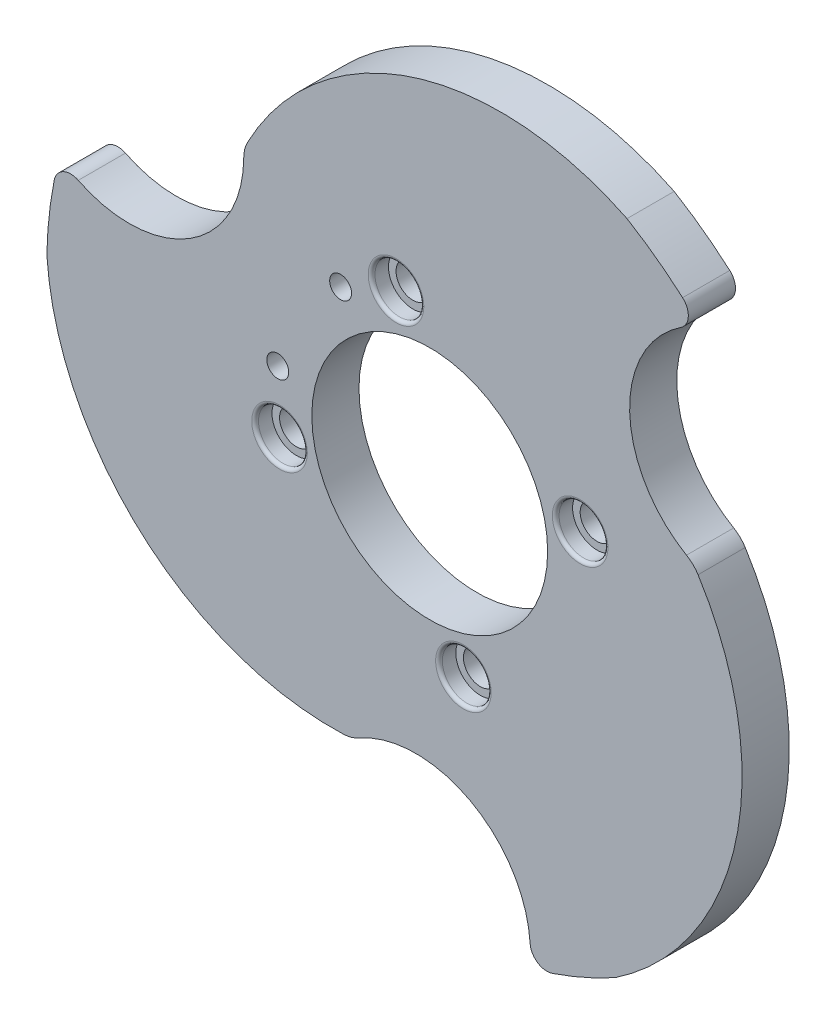
SolidWorks part; units mm, degrees
material "Nylon 101"
ref_plane "Front Plane" through (0, 0, 0) normal (0, 0, 1) x (1, 0, 0)
ref_plane "Top Plane" through (0, 0, 0) normal (0, 1, 0) x (1, 0, 0)
ref_plane "Right Plane" through (0, 0, 0) normal (1, 0, 0) x (0, 0, -1)
sketch "Sketch4" plane through (0, 0, 0) normal (0, 0, 1) x (1, 0, 0)
  line L0 (122.0825, 116.3897) -> (192.0825, 116.3897) construction
  line L1 (146.7212, 160.5313) -> (166.7236, 71.2444) construction
  arc A0 (231.7786, 201.237) -> (215.2728, 213.3033) centre (156.7224, 115.8878) ccw
  circle A1 centre (156.7224, 115.8878) radius 35
  arc A4 (102.6735, 176.6494) -> (215.2728, 213.3033) centre (177.8511, 136.9841) cw
  arc A5 (215.2728, 213.3033) -> (236.97, 196.3753) centre (156.7224, 115.8878) cw
  arc A7 (231.2424, 193.3169) -> (232.9372, 135.6297) centre (250.0433, 165.0007) ccw
  circle A8 centre (156.7224, 115.8878) radius 45.75 construction
  circle A9 centre (201.3658, 125.889) radius 5
  circle A10 centre (130.2738, 153.2179) radius 3.25
  circle A11 centre (166.7236, 71.2444) radius 5
  circle A12 centre (112.1469, 105.5881) radius 5
  circle A13 centre (146.7212, 160.5313) radius 5
  arc A14 (231.7786, 201.237) -> (231.2424, 193.3169) centre (228.4767, 197.4823) cw
  circle A15 centre (111.6251, 123.5881) radius 3.25
  arc A16 (186.5179, 12.637) -> (135.712, 40.0129) centre (152.595, 10.5131) ccw
  arc A17 (193.1088, 8.2126) -> (186.5179, 12.637) centre (191.5081, 12.9495) cw
  arc A18 (236.3679, 132.3147) -> (211.8114, 16.474) centre (164.428, 87.0417) cw
  arc A19 (193.1088, 8.2126) -> (211.8114, 16.474) centre (156.7224, 115.8878) ccw
  arc A20 (52.4068, 141.7095) -> (101.518, 172.0208) centre (67.5289, 172.1496) ccw
  arc A21 (45.2797, 138.2138) -> (52.4068, 141.7095) centre (50.1823, 137.2317) cw
  arc A22 (131.1257, 38.6993) -> (43.0829, 117.8862) centre (127.8881, 123.6376) cw
  arc A23 (45.2797, 138.2138) -> (43.0829, 117.8862) centre (156.7224, 115.8878) ccw
  arc A24 (232.9372, 135.6297) -> (236.3679, 132.3147) centre (227.9044, 126.9885) cw
  arc A25 (102.6735, 176.6494) -> (101.518, 172.0208) centre (111.5179, 171.9829) ccw
  arc A26 (135.712, 40.0129) -> (131.1257, 38.6993) centre (130.7448, 48.692) cw
  point P2 (236.97, 196.3753)
  point P3 (45.5812, 139.6691)
  point P4 (191.688, 7.7429)
  point P6 (48.1945, 141.391)
  point P8 (233.1808, 195.9929)
  point P9 (46.4024, 140.5065)
  point P10 (50.4833, 141.391)
  point P11 (53.7133, 140.5065)
  point P12 (58.5618, 139.2257)
  point P13 (61.9304, 138.4246)
  point P14 (65.3936, 137.8993)
  point P15 (68.3469, 137.8993)
  point P16 (72.7444, 138.4246)
  point P17 (74.802, 138.7777)
  point P18 (79.1471, 140.0693)
  point P19 (83.0146, 142.1289)
  point P20 (88.9812, 145.6229)
  point P21 (90.5528, 146.5796)
  point P22 (91.9878, 148.3562)
  point P23 (94.5844, 151.2945)
  point P24 (97.6436, 156.0404)
  point P25 (99.3422, 159.0902)
  point P26 (100.5527, 165.4783)
  point P27 (100.9923, 170.1847)
  point P28 (101.4578, 173.6239)
  point P29 (103.1795, 177.594)
  point P30 (104.9168, 180.4895)
  point P31 (109.9741, 187.9438)
  point P32 (117.4722, 196.5884)
  point P33 (128.1112, 205.827)
  point P34 (131.4763, 207.9055)
  point P35 (137.8833, 211.8266)
  point P36 (142.655, 214.4433)
  point P37 (147.8359, 216.6146)
  point P38 (152.6237, 218.2987)
  point P39 (155.9438, 219.1649)
  point P41 (166.9734, 221.3757)
  point P42 (177.9113, 221.7541)
  point P43 (184.4895, 221.3757)
  point P44 (189.0752, 220.8806)
  point P45 (196.3854, 219.622)
  point P46 (207.5547, 216.6146)
  point P47 (215.2728, 213.3033)
  point P52 (231.5123, 136.8636)
  point P53 (225.9479, 141.391)
  point P54 (235.0698, 134.4873)
  point P55 (221.8906, 146.5796)
  point P56 (221.8906, 184.0454)
  point P57 (218.3097, 152.8249)
  point P58 (225.6295, 188.576)
  point P59 (229.9403, 192.5766)
  point P62 (233.1808, 198.6008)
  point P64 (233.1808, 197.2257)
  point P69 (201.3658, 125.889)
  point P78 (156.7224, 115.8878)
  point P83 (236.97, 196.3753)
  point P102 (156.7224, 115.8878)
  dimension "D2" = 70
  dimension "D3" = 85
  dimension "D4" = 33.9894
  dimension "D5" = 91.5
  dimension "D6" = 10
  dimension "D7" = 6.5
  dimension "D9" = 5
  dimension "D10" = 18
  dimension "D8" = 6.5
  dimension "D12" = 10
  dimension "D14" = 10
  dimension "D15" = 10
  dimension "D16" = 10
  dimension "D1" = 70
  dimension "D11" = 18
  dimension "D13" = 3
extrude "Boss-Extrude2" add sketch "Sketch4" along normal blind 14 contours A26 A16 A17 A19 A18 A24 A7 A14 A0 A4 A25 A20 A21 A23 A22 A15 A13 A12 A11 A10 A9 A1
sketch "Sketch6" plane through (0, 0, 14) normal (0, 0, 1) x (1, 0, 0)
  circle A0 centre (130.2738, 153.2179) radius 3.25
  circle A1 centre (111.6251, 123.5881) radius 3.25
  dimension "D1" = 6.5
  dimension "D2" = 6.5
sketch "Esboço3" plane through (0, 0, 14) normal (0, 0, 1) x (1, 0, 0)
  circle A0 centre (201.3658, 125.889) radius 7.25
  circle A1 centre (146.7212, 160.5313) radius 7.25
  circle A2 centre (112.1469, 105.5881) radius 7.25
  circle A3 centre (166.7236, 71.2444) radius 7.25
  dimension "D1" = 14.5
extrude "Corte-extrusão1" cut sketch "Esboço3" against normal blind 5
fillet "Filete2" radius 1 4 edges at (208.6158, 125.889, 14) (173.9736, 71.2444, 14) (119.3969, 105.5881, 14) (153.9712, 160.5313, 14)
